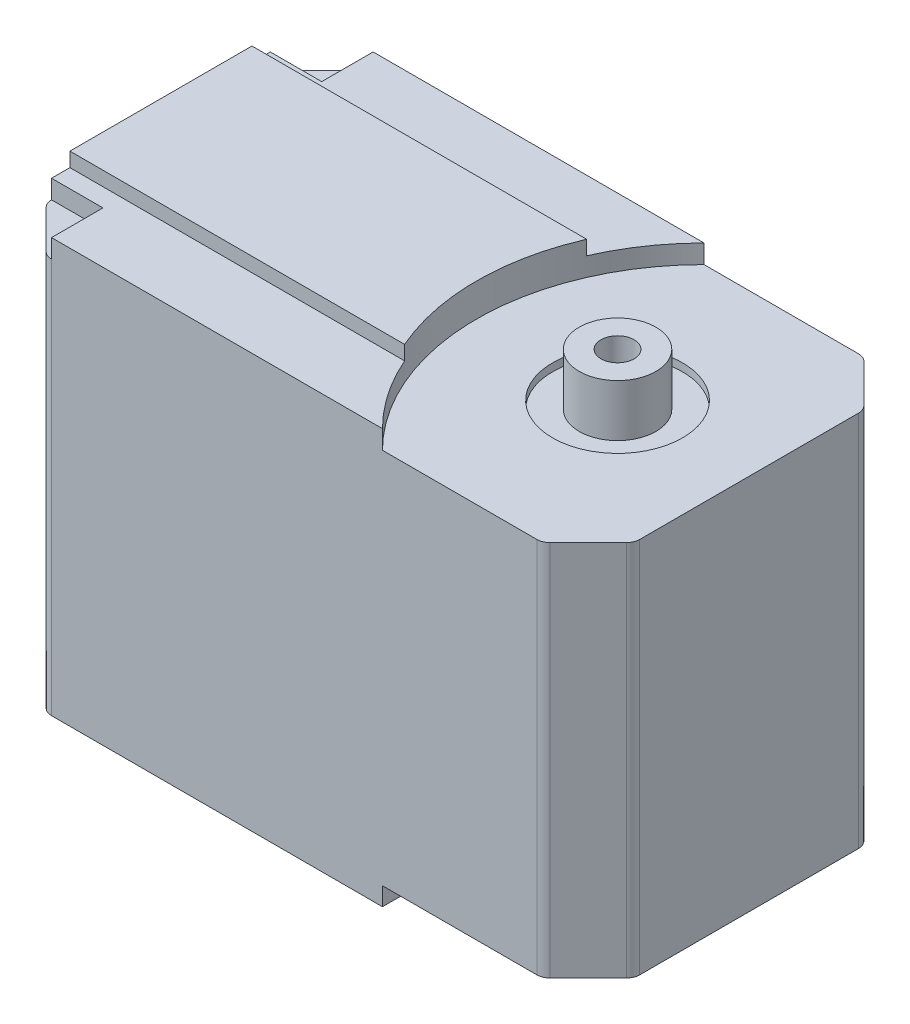
SolidWorks part; units mm, degrees
ref_plane "Ön Düzlem" through (0, 0, 0) normal (0, 0, 1) x (1, 0, 0)
ref_plane "Üst Düzlem" through (0, 0, 0) normal (0, 1, 0) x (1, 0, 0)
ref_plane "Sağ Düzlem" through (0, 0, 0) normal (1, 0, 0) x (0, 0, -1)
sketch "Çizim1" plane through (0, 0, 0) normal (0, 1, 0) x (1, 0, 0)
  line L1 (-22.615, -12.365) -> (22.615, -12.365)
  line L2 (-22.615, -12.365) -> (-22.615, 12.365)
  line L3 (-22.615, 12.365) -> (22.615, 12.365)
  line L4 (22.615, -12.365) -> (22.615, 12.365)
  line L5 (-22.615, -12.365) -> (22.615, 12.365) construction
  line L6 (-22.615, 12.365) -> (22.615, -12.365) construction
  point P0 (0, 0)
  dimension "D1" = 45.23
  dimension "D2" = 24.73
extrude "Yükseklik-Ekstrüzyon1" add sketch "Çizim1" along normal blind 29 contours L3 L4 L1 L2
chamfer "Pah1" distance 3.54 angle 45 4 edges at (-22.615, 14.5, -12.365) (-22.615, 14.5, 12.365) (22.615, 14.5, -12.365) (22.615, 14.5, 12.365)
fillet "Radyus1" radius 1 8 edges at (-22.615, 14.5, -8.825) (-19.075, 14.5, -12.365) (19.075, 14.5, -12.365) (22.615, 14.5, -8.825) (22.615, 14.5, 8.825) (19.075, 14.5, 12.365) (-19.075, 14.5, 12.365) (-22.615, 14.5, 8.825)
sketch "Çizim3" plane through (0, 29, 0) normal (0, 1, 0) x (1, 0, 0)
  line L0 (0, 12.365) -> (0, -12.365) construction
  line L1 (-18.6608, 12.365) -> (18.6608, 12.365) construction
  line L2 (-18.6608, -12.365) -> (18.6608, -12.365) construction
  line L3 (0, 0) -> (12.5, 0) construction
  circle A0 centre (12.5, 0) radius 5
  dimension "D2" = 10
  dimension "D1" = 12.5
extrude "Kes-Ekstrüzyon1" cut sketch "Çizim3" against normal blind 0.6
sketch "Çizim4" plane through (0, 28.4, 0) normal (0, 1, 0) x (1, 0, 0)
  circle A0 centre (12.5, 0) radius 2.95
  dimension "D1" = 5.9
extrude "Yükseklik-Ekstrüzyon2" add sketch "Çizim4" along normal blind 4
sketch "Çizim5" plane through (0, 32.4, 0) normal (0, 1, 0) x (1, 0, 0)
  circle A1 centre (12.5, 0) radius 1.275
  dimension "D1" = 2.55
extrude "Kes-Ekstrüzyon2" cut sketch "Çizim5" against normal blind 8
sketch "Çizim6" plane through (0, 29, 0) normal (0, 1, 0) x (1, 0, 0)
  line L0 (-22.615, 0) -> (1.385, 0) construction
  line L1 (-22.615, -8.4108) -> (-22.615, 8.4108) construction
  line L2 (6.785, -12.365) -> (-18.6608, -12.365)
  line L3 (-18.6608, -12.365) -> (18.6608, -12.365) construction
  line L4 (-18.6608, -12.365) -> (-18.6608, -8.4108)
  line L5 (-18.6608, -8.4108) -> (-22.615, -8.4108)
  line L6 (-18.6608, 8.4108) -> (-22.615, 8.4108)
  line L7 (-18.6608, 12.365) -> (-18.6608, 8.4108)
  line L8 (6.785, 12.365) -> (-18.6608, 12.365)
  line L9 (-22.615, 8.4108) -> (-22.615, -8.4108)
  arc A0 (6.785, 12.365) -> (6.785, -12.365) centre (19.15, 0) ccw
  dimension "D1" = 24
extrude "Yükseklik-Ekstrüzyon3" add sketch "Çizim6" along normal blind 1.44 contours L6 L9 L5 L4 L2 A0 L8 L7
sketch "Çizim7" plane through (0, 30.44, 0) normal (0, 1, 0) x (1, 0, 0)
  line L0 (-22.615, 8.4108) -> (-22.615, -8.4108) construction
  line L1 (-22.615, 7) -> (3.1254, 7)
  line L2 (-22.615, 7) -> (-22.615, -7)
  line L3 (-22.615, -7) -> (3.1254, -7)
  arc A0 (6.785, 12.365) -> (6.785, -12.365) centre (19.15, 0) ccw construction
  arc A1 (3.1254, 7) -> (3.1254, -7) centre (19.15, 0) ccw
  dimension "D1" = 14
  dimension "D2" = 7
extrude "Yükseklik-Ekstrüzyon4" add sketch "Çizim7" along normal blind 1.1
sketch "Çizim8" plane through (0, 0, 0) normal (0, -1, 0) x (1, 0, 0)
  line L0 (0, 0) -> (12.5, 0) construction
  circle A0 centre (12.5, 0) radius 3
  circle A1 centre (12.5, 0) radius 1.2
  dimension "D2" = 6
  dimension "D3" = 2.4
  dimension "D1" = 12.5
extrude "Yükseklik-Ekstrüzyon5" add sketch "Çizim8" along normal blind 4.1
sketch "Çizim9" plane through (0, 0, 0) normal (0, -1, 0) x (1, 0, 0)
  line L0 (-22.615, 0) -> (6.785, 0) construction
  line L1 (-22.615, 8.4108) -> (-22.615, -8.4108) construction
  line L2 (6.785, 12.365) -> (6.785, 9.165)
  line L3 (-18.6608, -12.365) -> (18.6608, -12.365) construction
  line L4 (6.785, -12.365) -> (-18.6608, -12.365)
  line L5 (-22.615, -8.4108) -> (-22.615, 8.4108)
  line L6 (-18.6608, 12.365) -> (6.785, 12.365)
  line L7 (-18.6608, 12.365) -> (18.6608, 12.365) construction
  line L8 (0.535, 9.765) -> (0.535, 6.615)
  line L9 (0.535, 6.615) -> (3.735, 6.615)
  line L10 (3.735, 6.615) -> (6.785, 9.165)
  line L11 (0.535, 9.765) -> (-4.265, 9.765)
  line L12 (-4.265, 9.765) -> (-4.265, -9.765)
  line L13 (6.785, -9.165) -> (6.785, -12.365)
  line L14 (0.535, -9.765) -> (-4.265, -9.765)
  line L15 (3.735, -6.615) -> (6.785, -9.165)
  line L16 (0.535, -6.615) -> (3.735, -6.615)
  line L17 (0.535, -9.765) -> (0.535, -6.615)
  line L18 (-19.3679, 12.0721) -> (-22.3221, 9.1179) construction
  line L19 (-19.3679, 12.0721) -> (-22.3221, 9.1179)
  line L20 (-22.3221, -9.1179) -> (-19.3679, -12.0721) construction
  line L21 (-22.3221, -9.1179) -> (-19.3679, -12.0721)
  arc A0 (-22.3221, 9.1179) -> (-22.615, 8.4108) centre (-21.615, 8.4108) ccw construction
  arc A1 (-18.6608, 12.365) -> (-19.3679, 12.0721) centre (-18.6608, 11.365) ccw construction
  arc A2 (-22.3221, 9.1179) -> (-22.615, 8.4108) centre (-21.615, 8.4108) ccw
  arc A3 (-18.6608, 12.365) -> (-19.3679, 12.0721) centre (-18.6608, 11.365) ccw
  arc A4 (-19.3679, -12.0721) -> (-18.6608, -12.365) centre (-18.6608, -11.365) ccw construction
  arc A5 (-22.615, -8.4108) -> (-22.3221, -9.1179) centre (-21.615, -8.4108) ccw construction
  arc A6 (-19.3679, -12.0721) -> (-18.6608, -12.365) centre (-18.6608, -11.365) ccw
  arc A7 (-22.615, -8.4108) -> (-22.3221, -9.1179) centre (-21.615, -8.4108) ccw
  point P19 (-4.265, 0)
  dimension "D1" = 29.4
  dimension "D2" = 6.25
  dimension "D3" = 3.2
  dimension "D4" = 2.6
  dimension "D5" = 3.2
  dimension "D6" = 4.8
extrude "Yükseklik-Ekstrüzyon6" add sketch "Çizim9" along normal blind 1.4 contours L19 A2 L5 A7 L21 A6 L4 L13 L15 L16 L17 L14 L12 L11 L8 L9 L10 L2 L6 A3
sketch "Çizim10" plane through (0, -1.4, 0) normal (0, -1, 0) x (1, 0, 0)
  line L0 (-4.265, 0) -> (-17.665, 0) construction
  line L1 (-4.265, 9.765) -> (-4.265, -9.765) construction
  line L3 (-17.665, 9.275) -> (-7.665, 9.275)
  line L4 (-17.665, 9.275) -> (-17.665, -9.275)
  line L5 (-17.665, -9.275) -> (-7.665, -9.275)
  line L6 (-7.665, 9.275) -> (-7.665, -9.275)
  dimension "D1" = 13.4
  dimension "D2" = 10
  dimension "D3" = 18.55
  dimension "D4" = 9.275
extrude "Yükseklik-Ekstrüzyon7" add sketch "Çizim10" along normal blind 1.83
sketch "Çizim11" plane through (0, 0, -9.275) normal (0, 0, -1) x (-1, 0, 0)
  line L0 (7.665, -3.23) -> (7.665, -1.4)
  line L1 (7.665, -1.4) -> (4.265, -1.4)
  line L2 (4.265, -1.4) -> (7.665, -3.23)
  dimension "D1" = 3.4
extrude "Yükseklik-Ekstrüzyon8" add sketch "Çizim11" against normal up to surface (18.55 mm away) up to face at (-12.665, -2.315, 9.275)
sketch "Çizim12" plane through (0, 0, 0) normal (0, -1, 0) x (1, 0, 0)
  line L0 (-4.265, 9.765) -> (-4.265, -9.765) construction
  line L1 (-4.265, 9.765) -> (-4.265, -9.765)
  line L2 (0.535, 9.765) -> (-4.265, 9.765) construction
  line L3 (0.535, 9.765) -> (-4.265, 9.765)
  line L4 (0.535, 9.765) -> (0.535, 6.615) construction
  line L5 (0.535, 9.765) -> (0.535, -9.765)
  line L6 (0.535, -9.765) -> (-4.265, -9.765) construction
  line L7 (0.535, -9.765) -> (-4.265, -9.765)
extrude "Kes-Ekstrüzyon3" cut sketch "Çizim12" against normal blind 9.38
sketch "Çizim13" plane through (0, 9.38, 0) normal (0, -1, 0) x (1, 0, 0)
  line L0 (0.535, 0) -> (-4.265, 0) construction
  line L1 (0.535, -9.765) -> (0.535, 9.765) construction
  line L2 (-4.265, 9.765) -> (-4.265, -9.765) construction
  line L3 (-4.265, 0.7) -> (0.535, 0.7) construction
  line L4 (-4.265, -0.7) -> (0.535, -0.7) construction
  line L5 (-4.265, 9.065) -> (0.535, 9.065) construction
  line L6 (0.535, 9.765) -> (-4.265, 9.765) construction
  line L7 (-0.165, 9.065) -> (-0.165, 0.7) construction
  line L10 (0.535, -6.615) -> (0.535, 6.615) construction
  line L11 (-3.565, 9.065) -> (-3.565, 0.7) construction
  line L12 (-4.265, 9.275) -> (-4.265, -9.275) construction
  line L13 (-3.565, 4.8825) -> (-0.165, 4.8825) construction
  line L14 (-3.565, 6.9725) -> (-0.165, 6.9725) construction
  line L15 (-1.515, 4.5325) -> (-0.815, 4.5325)
  line L16 (-1.515, 4.5325) -> (-1.515, 5.2325)
  line L17 (-1.515, 5.2325) -> (-0.815, 5.2325)
  line L18 (-0.815, 4.5325) -> (-0.815, 5.2325)
  line L19 (-1.515, 4.5325) -> (-0.815, 5.2325) construction
  line L20 (-1.515, 5.2325) -> (-0.815, 4.5325) construction
  line L21 (-3.565, 2.7925) -> (-0.165, 2.7925) construction
  line L22 (-1.515, 6.6225) -> (-0.815, 6.6225)
  line L23 (-1.515, 6.6225) -> (-1.515, 7.3225)
  line L24 (-1.515, 7.3225) -> (-0.815, 7.3225)
  line L25 (-0.815, 6.6225) -> (-0.815, 7.3225)
  line L26 (-1.515, 6.6225) -> (-0.815, 7.3225) construction
  line L27 (-1.515, 7.3225) -> (-0.815, 6.6225) construction
  line L28 (-1.515, -3.1425) -> (-0.815, -2.4425) construction
  line L29 (-1.515, 2.4425) -> (-0.815, 2.4425)
  line L30 (-1.515, 2.4425) -> (-1.515, 3.1425)
  line L31 (-1.515, 3.1425) -> (-0.815, 3.1425)
  line L32 (-0.815, 2.4425) -> (-0.815, 3.1425)
  line L33 (-1.515, 2.4425) -> (-0.815, 3.1425) construction
  line L34 (-1.515, 3.1425) -> (-0.815, 2.4425) construction
  line L35 (-1.515, -2.4425) -> (-0.815, -3.1425) construction
  line L36 (-1.515, -7.3225) -> (-0.815, -6.6225) construction
  line L37 (-1.515, -6.6225) -> (-0.815, -7.3225) construction
  line L38 (-1.515, -5.2325) -> (-0.815, -4.5325) construction
  line L39 (-1.515, -4.5325) -> (-0.815, -5.2325) construction
  line L40 (-0.815, -2.4425) -> (-0.815, -3.1425)
  line L41 (-1.515, -3.1425) -> (-0.815, -3.1425)
  line L42 (-1.515, -2.4425) -> (-1.515, -3.1425)
  line L43 (-1.515, -2.4425) -> (-0.815, -2.4425)
  line L44 (-0.815, -6.6225) -> (-0.815, -7.3225)
  line L45 (-1.515, -7.3225) -> (-0.815, -7.3225)
  line L46 (-1.515, -6.6225) -> (-1.515, -7.3225)
  line L47 (-1.515, -6.6225) -> (-0.815, -6.6225)
  line L48 (-0.815, -4.5325) -> (-0.815, -5.2325)
  line L49 (-1.515, -5.2325) -> (-0.815, -5.2325)
  line L50 (-1.515, -4.5325) -> (-1.515, -5.2325)
  line L51 (-1.515, -4.5325) -> (-0.815, -4.5325)
  point P25 (-1.165, 4.8825)
  point P32 (-1.165, 6.9725)
  point P39 (-1.165, 2.7925)
  point P56 (-1.165, -2.7925)
  point P57 (-1.165, -6.9725)
  point P58 (-1.165, -4.8825)
  dimension "D1" = 0.7
  dimension "D2" = 0.7
  dimension "D3" = 0.7
  dimension "D4" = 0.7
  dimension "D5" = 0.7
  dimension "D6" = 0.7
  dimension "D7" = 0.7
  dimension "D8" = 1
  dimension "D9" = 2.09
  dimension "D10" = 0.7
  dimension "D11" = 0.7
  dimension "D12" = 1
  dimension "D13" = 2.09
  dimension "D14" = 1
  dimension "D15" = 0.7
  dimension "D16" = 0.7
extrude "Yükseklik-Ekstrüzyon9" add sketch "Çizim13" along normal blind 3.59
sketch "Çizim14" plane through (0, 9.38, 0) normal (0, -1, 0) x (1, 0, 0)
  line L0 (-0.165, 9.065) -> (-3.565, 9.065)
  line L1 (-3.565, 9.065) -> (-3.565, 0.6579)
  line L2 (-3.565, -9.065) -> (-0.165, -9.065)
  line L3 (-0.165, -9.065) -> (-0.165, -0.9421)
  line L4 (0.535, 9.765) -> (-4.265, 9.765)
  line L5 (-4.265, 9.765) -> (-4.265, -9.765)
  line L6 (-4.265, -9.765) -> (0.535, -9.765)
  line L7 (0.535, -9.765) -> (0.535, 9.765)
  line L8 (0.535, 9.765) -> (-4.265, 9.765)
  line L9 (-4.265, 9.765) -> (-4.265, -0.0421)
  line L10 (-4.265, -9.765) -> (0.535, -9.765)
  line L11 (0.535, -9.765) -> (0.535, -0.2421)
  line L12 (-4.265, -0.1421) -> (0.535, -0.1421) construction
  line L13 (-4.265, -0.0421) -> (0.535, -0.0421)
  line L14 (-4.265, -0.2421) -> (-4.265, -9.765)
  line L15 (-3.565, -0.9421) -> (-3.565, -9.065)
  line L16 (-4.265, 9.765) -> (-4.265, -9.765) construction
  line L17 (-0.165, 0.6579) -> (-0.165, 9.065)
  line L18 (-3.565, 9.065) -> (-3.565, -9.065) construction
  line L19 (0.535, -0.0421) -> (0.535, 9.765)
  line L20 (-0.165, -9.065) -> (-0.165, 9.065) construction
  line L21 (-3.565, 0.6579) -> (-0.165, 0.6579)
  line L22 (0.535, -9.765) -> (0.535, 9.765) construction
  line L23 (-4.265, -0.2421) -> (0.535, -0.2421)
  line L24 (-3.565, -0.9421) -> (-0.165, -0.9421)
  dimension "D3" = 0.1
  dimension "D4" = 0.7
  dimension "D5" = 0.1
  dimension "D6" = 0.7
  dimension "D1" = 0
  dimension "D2" = 0.7
extrude "Yükseklik-Ekstrüzyon10" add sketch "Çizim14" along normal blind 4.59
